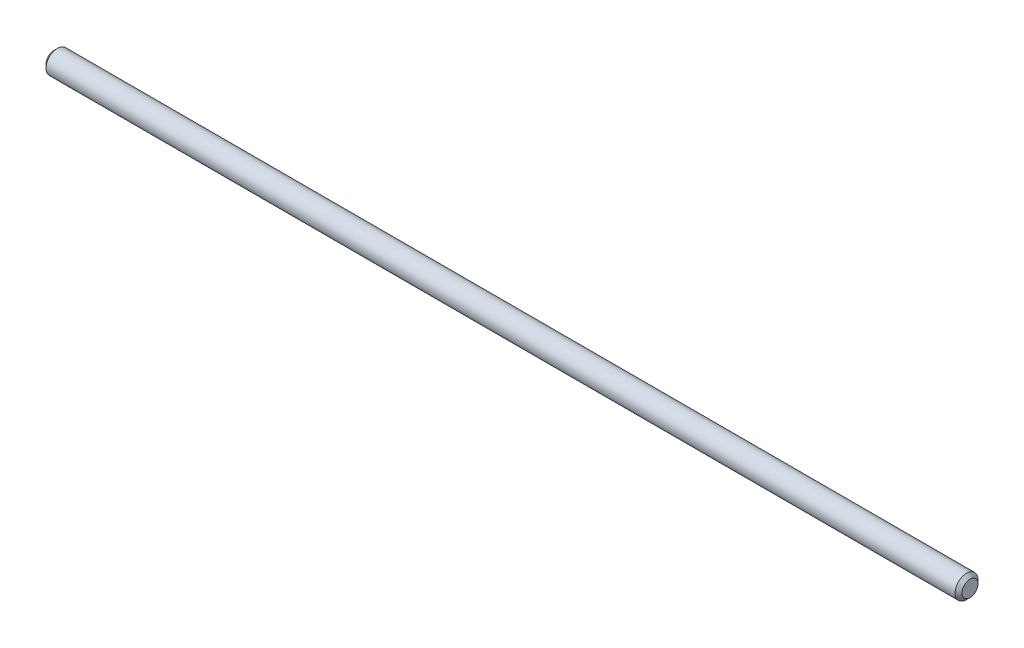
SolidWorks part; units mm, degrees
material "1.0037 (S235JR)"
ref_plane "Front Plane" through (0, 0, 0) normal (0, 0, 1) x (1, 0, 0)
ref_plane "Top Plane" through (0, 0, 0) normal (0, 1, 0) x (1, 0, 0)
ref_plane "Right Plane" through (0, 0, 0) normal (1, 0, 0) x (0, 0, -1)
sketch "Sketch1" plane through (0, 0, 0) normal (0, 0, 1) x (1, 0, 0)
  line L0 (-457.1351, 0) -> (985.5614, 0) construction
  line L1 (0, 0) -> (0, 10)
  line L2 (0, 10) -> (800, 10)
  line L3 (800, 10) -> (800, 0)
  line L4 (0, 0) -> (800, 0)
  dimension "D1" = 800
  dimension "D2" = 20
revolve "Revolve1" add sketch "Sketch1" angle 360 about L0
chamfer "Chamfer1" distance 3 angle 45 2 edges at (800, 0, 10) (0, 0, 10)
